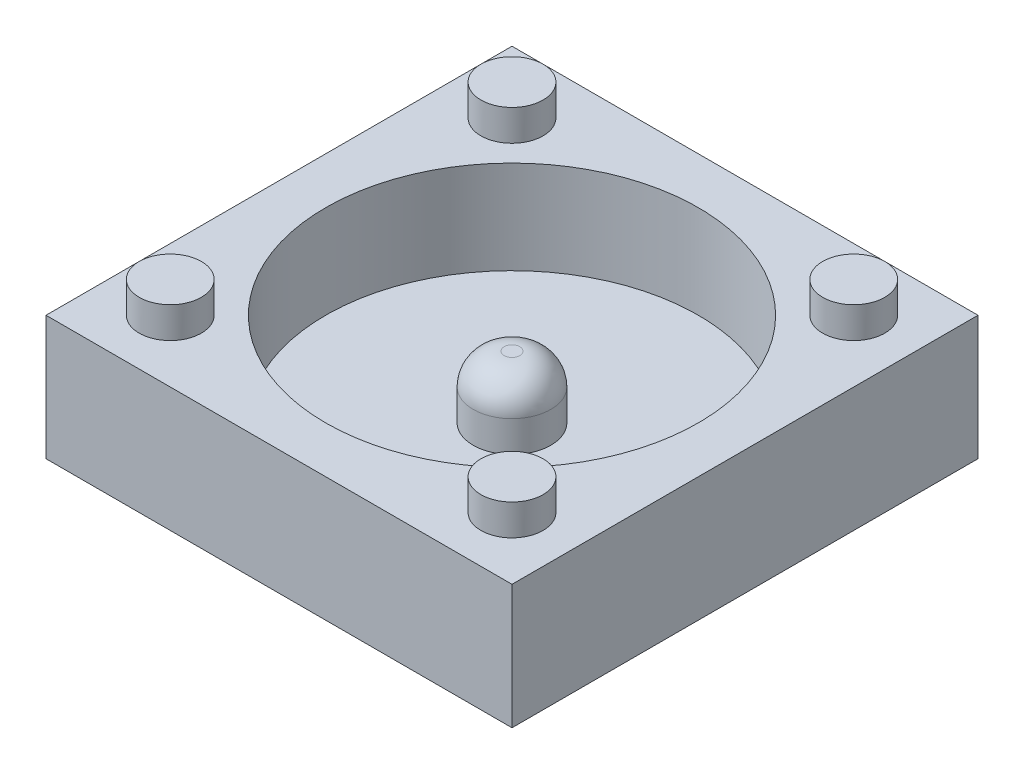
SolidWorks part; units mm, degrees
ref_plane "Front Plane" through (0, 0, 0) normal (0, 0, 1) x (1, 0, 0)
ref_plane "Top Plane" through (0, 0, 0) normal (0, 1, 0) x (1, 0, 0)
ref_plane "Right Plane" through (0, 0, 0) normal (1, 0, 0) x (0, 0, -1)
sketch "Sketch1" plane through (0, 0, 0) normal (0, 1, 0) x (1, 0, 0)
  line L1 (-7.5, -7.5) -> (7.5, -7.5)
  line L2 (-7.5, -7.5) -> (-7.5, 7.5)
  line L3 (-7.5, 7.5) -> (7.5, 7.5)
  line L4 (7.5, -7.5) -> (7.5, 7.5)
  line L5 (-7.5, -7.5) -> (7.5, 7.5) construction
  line L6 (-7.5, 7.5) -> (7.5, -7.5) construction
  point P0 (0, 0)
  dimension "D1" = 15
  dimension "D2" = 15
extrude "Boss-Extrude2" add sketch "Sketch1" along normal blind 4
sketch "Sketch4" plane through (0, 4, 0) normal (0, 1, 0) x (1, 0, 0)
  circle A0 centre (0, 0) radius 6
  dimension "D1" = 12
extrude "Cut-Extrude4" cut sketch "Sketch4" against normal blind 3
sketch "Sketch5" plane through (0, 1, 0) normal (0, 1, 0) x (1, 0, 0)
  circle A0 centre (0, 0) radius 1.25
  dimension "D1" = 2.5
extrude "Boss-Extrude3" add sketch "Sketch5" along normal blind 2
fillet "Fillet2" radius 1 1 edges at (0, 3, 1.25)
sketch "Sketch6" plane through (0, 4, 0) normal (0, 1, 0) x (1, 0, 0)
  line L0 (-7.5, 7.5) -> (-7.5, -7.5) construction
  line L1 (7.5, 7.5) -> (-7.5, 7.5) construction
  line L2 (7.5, -7.5) -> (7.5, 7.5) construction
  line L3 (-7.5, -7.5) -> (7.5, -7.5) construction
  circle A0 centre (-5.5, 5.5) radius 1
  circle A1 centre (5.5, 5.5) radius 1
  circle A2 centre (-5.5, -5.5) radius 1
  circle A3 centre (5.5, -5.5) radius 1
  dimension "D1" = 2
  dimension "D4" = 2
  dimension "D7" = 2
  dimension "D10" = 2
  dimension "D2" = 2
  dimension "D3" = 2
  dimension "D5" = 2
  dimension "D6" = 2
  dimension "D8" = 2
  dimension "D9" = 2
  dimension "D11" = 2
  dimension "D12" = 2
extrude "Boss-Extrude4" add sketch "Sketch6" along normal blind 1
